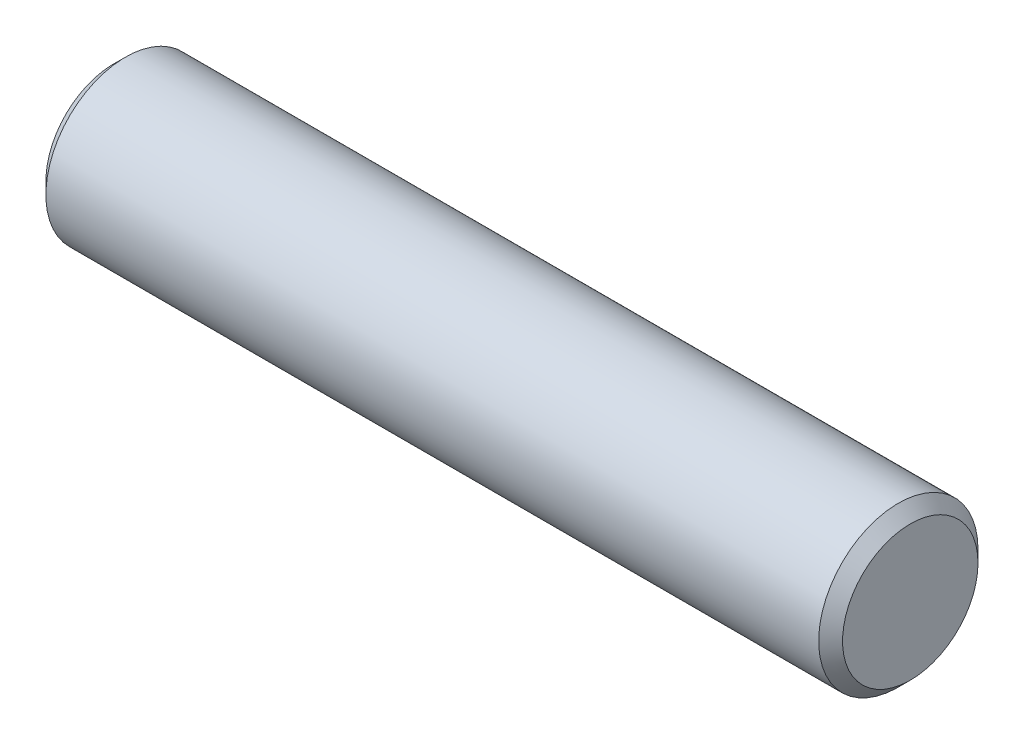
SolidWorks part; units mm, degrees
revolve "BaseBody" add sketch "BodySke" angle 360 about L14
sketch "BodySke" plane through (0, 0, 0) normal (0, 0, 1) x (1, 0, 0)
  line L0 (83, 15.875) -> (83, -6.35) construction
  line L1 (2.5, 15.875) -> (2.5, -3.175) construction
  line L2 (95, 6.35) -> (95, 3.175) construction
  line L10 (0, 10) -> (100, 10)
  line L12 (100, 10) -> (100, 0)
  line L13 (100, 0) -> (0, 0)
  line L14 (-3.175, 0) -> (107.95, 0) construction
  line L18 (0, 10) -> (0, 0)
cosmetic thread "ThreadCosmetic" [suppressed] parameters "Thread_minor"=17
ref_plane "Plane1" through (0, 0, 0) normal (0, 0, 1) x (1, 0, 0)
ref_plane "Plane2" through (0, 0, 0) normal (0, 1, 0) x (1, 0, 0)
ref_plane "Plane3" through (0, 0, 0) normal (1, 0, 0) x (0, 0, -1)
other "Configuration Table"
chamfer "Chamfer1" distance 1.5 angle 45 2 edges at (100, 0, 10) (0, 0, 10)
sketch "ThdSchSke" plane through (0, 0, 0) normal (0, 0, 1) x (1, 0, 0)
  line L0 (1.0503, -8.5) -> (0, -10)
  line L1 (1.0503, -8.5) -> (2.1006, -10)
  line L2 (2.1006, -10) -> (2.1006, -12.5)
  line L3 (-3.175, 0) -> (5.1513, 0) construction
  line L4 (0, 10) -> (0, -10) construction
  line L5 (2.1006, -12.5) -> (0, -12.5)
  line L6 (0, -12.5) -> (0, -10)
revolve "ThreadSchematic" [suppressed] cut sketch "ThdSchSke" angle 360 about L3
pattern_linear "ThdSchPat" [suppressed]
equation "\"Thread_minor@ThreadCosmetic\" = \"Minor_dia@BodySke\""
equation "\"Chamfer@Chamfer1\" =  ( \"Diameter@BodySke\" - \"Minor_dia@BodySke\" ) / 2"
equation "\"Thread_minor@ThdSchSke\" = \"Minor_dia@BodySke\""
equation "\"Diameter@ThdSchSke\" = \"Diameter@BodySke\""
equation "\"Overcut@ThdSchSke\" = \"Diameter@BodySke\" * 1.25"
equation "\"Num_threads@ThdSchPat\" = int( (\"Thread_max@BodySke\" - \"Advance@BodySke\" ) / \"Advance@BodySke\" + 0.999 ) + 1"
equation "\"Advance@ThdSchPat\" = \"Thread_max@BodySke\" /  ( \"Num_threads@ThdSchPat\" - 1 ) 'relax it"
equation "\"Num_threads@ThdSchPat\" = \"Num_threads@ThdSchPat\" - sgn( \"Num_threads@ThdSchPat\" - 1 ) '---chamfered tips only---"
